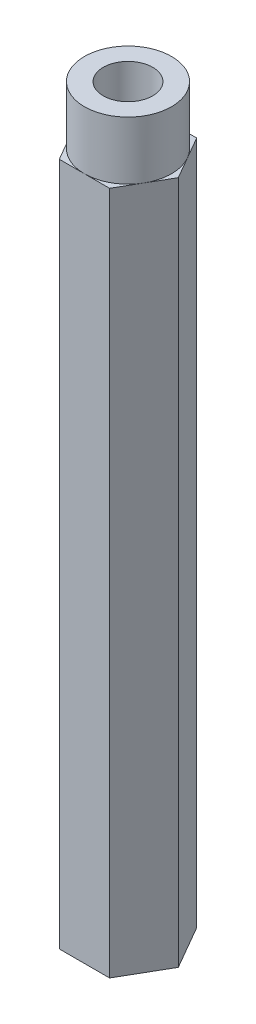
SolidWorks part; units mm, degrees
material "Alum Plate"
ref_plane "Front Plane" through (0, 0, 0) normal (0, 0, 1) x (1, 0, 0)
ref_plane "Top Plane" through (0, 0, 0) normal (0, 1, 0) x (1, 0, 0)
ref_plane "Right Plane" through (0, 0, 0) normal (1, 0, 0) x (0, 0, -1)
sketch "Sketch1" plane through (0, 0, 0) normal (0, 1, 0) x (1, 0, 0)
  line L1 (1.3748, -2.3812) -> (2.7496, 0)
  line L2 (2.7496, 0) -> (1.3748, 2.3813)
  line L3 (1.3748, 2.3813) -> (-1.3748, 2.3813)
  line L4 (-1.3748, 2.3813) -> (-2.7496, 0)
  line L5 (-2.7496, 0) -> (-1.3748, -2.3812)
  line L6 (-1.3748, -2.3812) -> (1.3748, -2.3812)
  circle A0 centre (0, 0) radius 2.3812 construction
  dimension "D1" = 4.7625
extrude "Boss-Extrude1" add sketch "Sketch1" along normal mid plane 37.3888
sketch "Sketch2" plane through (0, 18.6944, 0) normal (0, 1, 0) x (1, 0, 0)
  line L0 (1.3748, -2.3812) -> (2.7496, 0) construction
  circle A0 centre (0, 0) radius 2.3812
extrude "Boss-Extrude2" add sketch "Sketch2" along normal blind 3.175
sketch "Sketch3" plane through (0, 21.8694, 0) normal (0, 1, 0) x (1, 0, 0)
  circle A0 centre (0, 0) radius 1.3525
  dimension "D1" = 2.7051
extrude "Cut-Extrude1" cut sketch "Sketch3" against normal blind 6.35
